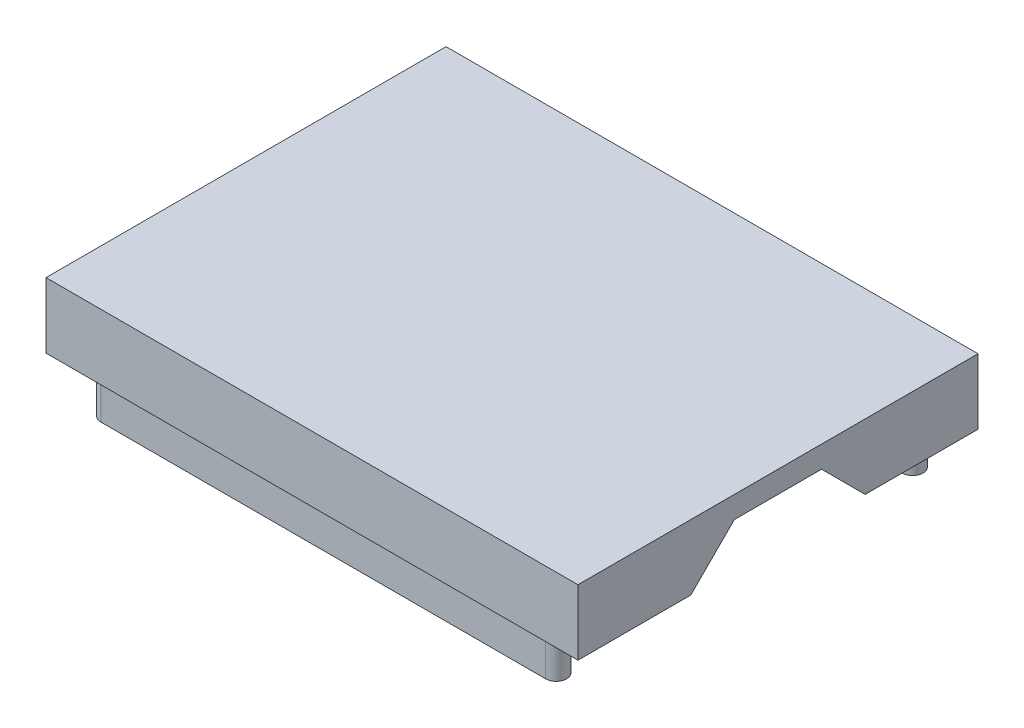
SolidWorks part; units mm, degrees
ref_plane "Front Plane" through (0, 0, 0) normal (0, 0, 1) x (1, 0, 0)
ref_plane "Top Plane" through (0, 0, 0) normal (0, 1, 0) x (1, 0, 0)
ref_plane "Right Plane" through (0, 0, 0) normal (1, 0, 0) x (0, 0, -1)
sketch "Sketch1" plane through (0, 0, 0) normal (0, 1, 0) x (1, 0, 0)
  line L1 (0, 0) -> (30.988, 0)
  line L2 (0, 0) -> (0, 23.3045)
  line L3 (0, 23.3045) -> (30.988, 23.3045)
  line L4 (30.988, 0) -> (30.988, 23.3045)
  dimension "D1" = 23.3045
  dimension "D2" = 30.988
extrude "Boss-Extrude1" add sketch "Sketch1" along normal blind 3.81
sketch "Sketch2" plane through (30.988, 0, 0) normal (1, 0, 0) x (0, 0, -1)
  line L0 (6.5722, 0) -> (9.1122, 2.54)
  line L1 (0, 0) -> (23.3045, 0) construction
  line L2 (9.1122, 2.54) -> (14.1922, 2.54)
  line L3 (14.1922, 2.54) -> (16.7323, 0)
  line L4 (6.5722, 0) -> (16.7323, 0)
  point P5 (11.6522, 2.54)
  point P7 (11.6522, 0)
  dimension "D1" = 10.16
  dimension "D2" = 5.08
  dimension "D3" = 2.54
extrude "Cut-Extrude1" cut sketch "Sketch2" against normal blind 29.718
sketch "Sketch3" plane through (0, 0, 0) normal (0, -1, 0) x (1, 0, 0)
  line L0 (2.54, -1.27) -> (28.448, -1.27) construction
  line L1 (2.54, -0.6604) -> (28.448, -0.6604)
  line L2 (2.54, -1.8796) -> (28.448, -1.8796)
  line L3 (2.54, -22.0345) -> (28.448, -22.0345) construction
  line L4 (2.54, -21.4249) -> (28.448, -21.4249)
  line L5 (2.54, -22.6441) -> (28.448, -22.6441)
  line L6 (30.988, -23.3045) -> (0, -23.3045) construction
  line L7 (0, 0) -> (30.988, 0) construction
  line L8 (30.988, 0) -> (30.988, -6.5722) construction
  line L9 (0, -23.3045) -> (0, 0) construction
  line L10 (30.988, -16.7323) -> (30.988, -23.3045) construction
  arc A0 (2.54, -0.6604) -> (2.54, -1.8796) centre (2.54, -1.27) ccw
  arc A1 (28.448, -1.8796) -> (28.448, -0.6604) centre (28.448, -1.27) ccw
  arc A2 (2.54, -21.4249) -> (2.54, -22.6441) centre (2.54, -22.0345) ccw
  arc A3 (28.448, -22.6441) -> (28.448, -21.4249) centre (28.448, -22.0345) ccw
  point P2 (15.494, -1.27)
  point P7 (15.494, -22.0345)
  dimension "D1" = 0.6096
  dimension "D2" = 0.6096
  dimension "D3" = 1.27
  dimension "D4" = 1.27
  dimension "D5" = 2.54
  dimension "D6" = 2.54
  dimension "D7" = 2.54
  dimension "D8" = 2.54
  dimension "D9" = 20.7645
extrude "Boss-Extrude2" add sketch "Sketch3" along normal blind 2.54
sketch "Sketch4" plane through (0, 0, 0) normal (0, -1, 0) x (1, 0, 0)
  line L0 (0, -23.3045) -> (0, 0) construction
  line L1 (2.54, -20.7645) -> (28.448, -20.7645)
  line L2 (2.54, -20.7645) -> (2.54, -2.54)
  line L3 (2.54, -2.54) -> (28.448, -2.54)
  line L4 (28.448, -20.7645) -> (28.448, -2.54)
  line L5 (30.988, 0) -> (30.988, -6.5722) construction
  line L6 (30.988, -23.3045) -> (0, -23.3045) construction
  dimension "D1" = 18.2245
  dimension "D2" = 25.908
  dimension "D3" = 2.54
  dimension "D4" = 2.54
  dimension "D5" = 2.54
extrude "Cut-Extrude2" cut sketch "Sketch4" against normal blind 2.54
